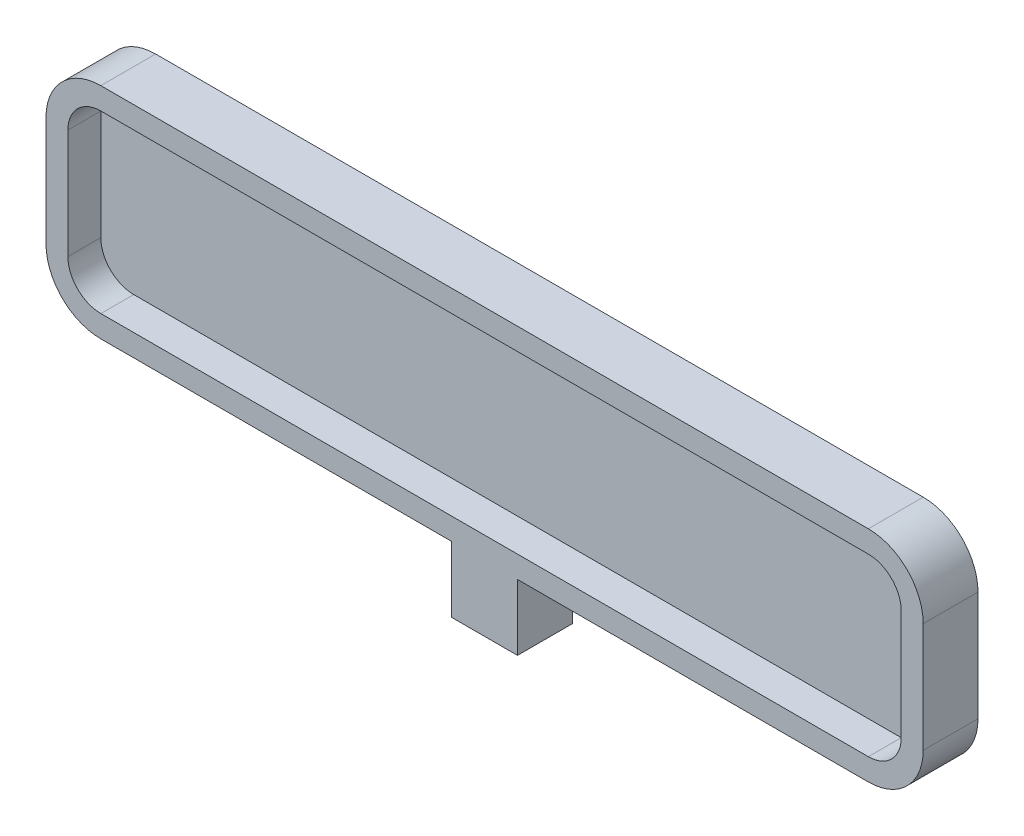
SolidWorks part; units mm, degrees
ref_plane "Front Plane" through (0, 0, 0) normal (0, 0, 1) x (1, 0, 0)
ref_plane "Top Plane" through (0, 0, 0) normal (0, 1, 0) x (1, 0, 0)
ref_plane "Right Plane" through (0, 0, 0) normal (1, 0, 0) x (0, 0, -1)
sketch "Sketch2" plane through (0, 0, 0) normal (0, 0, 1) x (1, 0, 0)
  line L1 (40, 10) -> (-40, 10)
  line L2 (40, 10) -> (40, -10)
  line L3 (40, -10) -> (-40, -10)
  line L4 (-40, 10) -> (-40, -10)
  line L5 (40, 10) -> (-40, -10) construction
  line L6 (40, -10) -> (-40, 10) construction
  point P1 (0, 0)
  dimension "D1" = 80
  dimension "D2" = 20
extrude "Boss-Extrude1" add sketch "Sketch2" along normal blind 5
fillet "Fillet1" radius 5 4 edges at (-40, -10, 2.5) (40, -10, 2.5) (40, 10, 2.5) (-40, 10, 2.5)
shell "Shell1" thickness 2
sketch "Sketch3" plane through (0, -10, 0) normal (0, -1, 0) x (1, 0, 0)
  line L0 (-35, 5) -> (35, 5) construction
  line L1 (-3, 0) -> (3, 0)
  line L2 (-3, 0) -> (-3, 5)
  line L3 (-3, 5) -> (3, 5)
  line L4 (3, 0) -> (3, 5)
  line L5 (-3, 0) -> (3, 5) construction
  line L6 (-3, 5) -> (3, 0) construction
  line L7 (0, 0) -> (0, 5) construction
  point P0 (0, 2.5)
  point P10 (0, 0)
  dimension "D1" = 5
  dimension "D2" = 6
extrude "Boss-Extrude2" add sketch "Sketch3" along normal blind 6
sketch "Sketch4" plane through (0, -16, 0) normal (0, -1, 0) x (1, 0, 0)
  line L0 (3, 0) -> (3, 5) construction
  line L1 (3, 5) -> (-3, 5) construction
  circle A0 centre (0, 2.5) radius 1.425
  dimension "D1" = 2.85
  dimension "D2" = 3
  dimension "D3" = 2.5
extrude "Cut-Extrude1" cut sketch "Sketch4" against normal blind 4
